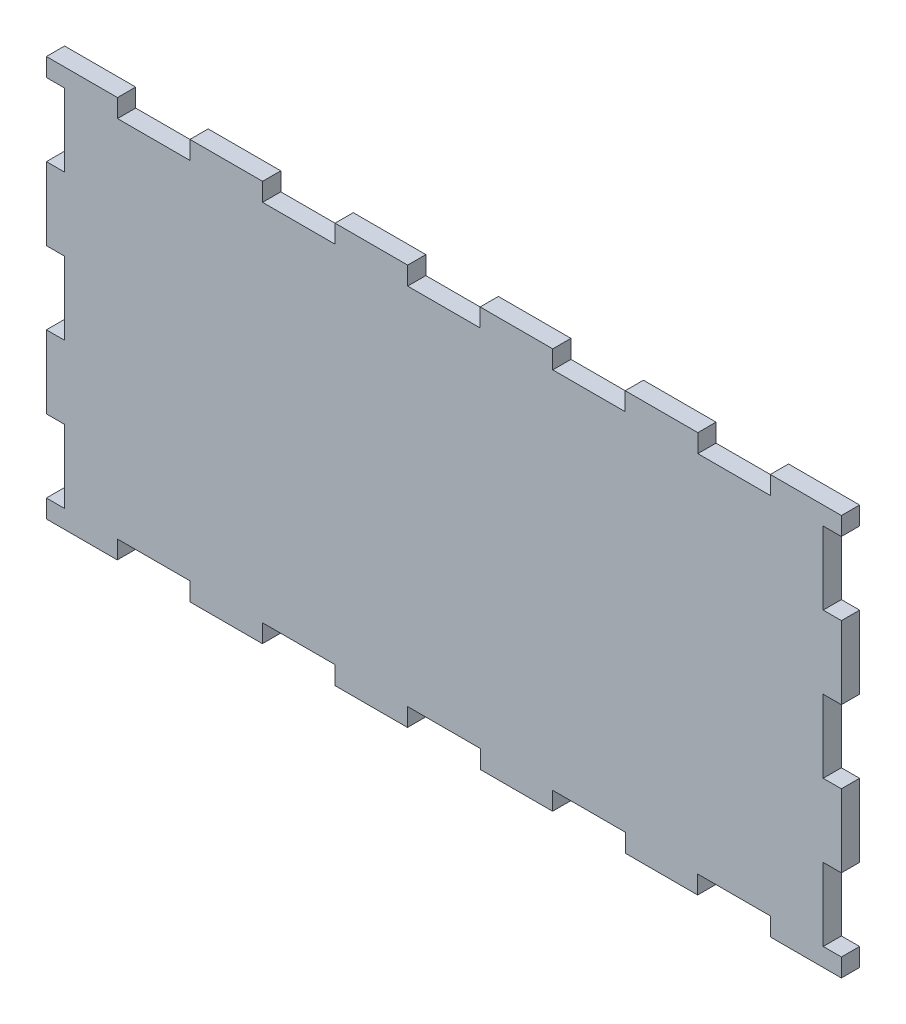
SolidWorks part; units mm, degrees
ref_plane "Front Plane" through (0, 0, 0) normal (0, 0, 1) x (1, 0, 0)
ref_plane "Top Plane" through (0, 0, 0) normal (0, 1, 0) x (1, 0, 0)
ref_plane "Right Plane" through (0, 0, 0) normal (1, 0, 0) x (0, 0, -1)
sketch "Sketch2" plane through (0, 0, 0) normal (0, 0, 1) x (1, 0, 0)
  line L0 (-65.4714, 3) -> (-53.7868, 3)
  line L1 (-53.7868, 3) -> (-53.7868, 6)
  line L2 (-53.7868, 6) -> (-41.7868, 6)
  line L3 (-41.7868, 6) -> (-41.7868, 3)
  line L4 (-41.7868, 3) -> (-29.8791, 3)
  line L5 (-29.8791, 3) -> (-29.8791, 6)
  line L6 (-29.8791, 6) -> (-17.8791, 6)
  line L7 (-17.8791, 6) -> (-17.8791, 3)
  line L8 (-17.8791, 3) -> (-5.9714, 3)
  line L9 (-5.9714, 3) -> (-5.9714, 6)
  line L10 (-5.9714, 6) -> (6.0286, 6)
  line L11 (6.0286, 6) -> (6.0286, 3)
  line L12 (6.0286, 3) -> (17.9363, 3)
  line L13 (17.9363, 3) -> (17.9363, 6)
  line L14 (17.9363, 6) -> (29.9363, 6)
  line L15 (29.9363, 6) -> (29.9363, 3)
  line L16 (29.9363, 3) -> (41.844, 3)
  line L17 (41.844, 3) -> (41.844, 6)
  line L18 (41.844, 6) -> (53.844, 6)
  line L19 (53.844, 6) -> (53.844, 3)
  line L20 (53.844, 3) -> (65.5286, 3)
  line L21 (65.5286, 3) -> (65.5286, 69)
  line L22 (-65.4714, 3) -> (-65.4714, 69)
  line L24 (53.8154, 69) -> (65.5286, 69)
  line L25 (53.8154, 66) -> (53.8154, 69)
  line L26 (41.8725, 66) -> (53.8154, 66)
  line L27 (41.8725, 69) -> (41.8725, 66)
  line L28 (29.9077, 69) -> (41.8725, 69)
  line L29 (29.9077, 66) -> (29.9077, 69)
  line L30 (17.9648, 66) -> (29.9077, 66)
  line L31 (17.9648, 69) -> (17.9648, 66)
  line L32 (6, 69) -> (17.9648, 69)
  line L33 (6, 66) -> (6, 69)
  line L34 (-5.9429, 66) -> (6, 66)
  line L35 (-5.9429, 69) -> (-5.9429, 66)
  line L36 (-17.9077, 69) -> (-5.9429, 69)
  line L37 (-17.9077, 66) -> (-17.9077, 69)
  line L38 (-29.8505, 66) -> (-17.9077, 66)
  line L39 (-29.8505, 69) -> (-29.8505, 66)
  line L40 (-41.8154, 69) -> (-29.8505, 69)
  line L41 (-41.8154, 66) -> (-41.8154, 69)
  line L42 (-53.7582, 66) -> (-41.8154, 66)
  line L43 (-53.7582, 69) -> (-53.7582, 66)
  line L44 (-65.4714, 69) -> (-53.7582, 69)
  line M1 (-54, 0) -> (-54, 6)
  line M2 (-54, 6) -> (-62.5, 6)
  line M3 (-62.5, 6) -> (-62.5, 0)
  dimension "D1" = 60
  dimension "D2" = 3
  dimension "D3" = 12
  dimension "D4" = 131
extrude "Boss-Extrude1" add sketch "Sketch2" along normal blind 3 contours L0 M3 M1 M2 | L44 L22 L0 L2 L3 L4 L5 L6 L7 L8 L9 L10 L11 L12 L13 L14 L15 L16 L17 L18 L19 L20 L21 L24 L25 L26 L27 L28 L29 L30 L31 L32 L33 L34 L35 L36 L37 L38 L39 L40 L41 L42 L43 M3 M2
sketch "Sketch3" plane through (0, 0, 3) normal (0, 0, 1) x (1, 0, 0)
  line L0 (-65.4714, 3) -> (-65.4714, 69) construction
  line L1 (-65.4714, 6) -> (-62.4714, 6)
  line L2 (-65.4714, 6) -> (-65.4714, 18)
  line L3 (-65.4714, 18) -> (-62.4714, 18)
  line L4 (-62.4714, 6) -> (-62.4714, 18)
  line L5 (62.5286, 6) -> (62.5286, 18)
  line L6 (62.5286, 6) -> (65.5286, 6)
  line L7 (65.5286, 6) -> (65.5286, 18)
  line L8 (62.5286, 18) -> (65.5286, 18)
  line L9 (62.5286, 30) -> (62.5286, 42)
  line L10 (62.5286, 30) -> (65.5286, 30)
  line L11 (65.5286, 30) -> (65.5286, 42)
  line L12 (62.5286, 42) -> (65.5286, 42)
  line L13 (62.5286, 54) -> (62.5286, 66)
  line L14 (62.5286, 54) -> (65.5286, 54)
  line L15 (65.5286, 54) -> (65.5286, 66)
  line L16 (62.5286, 66) -> (65.5286, 66)
  line L17 (-65.4714, 30) -> (-65.4714, 42)
  line L18 (-65.4714, 30) -> (-62.4714, 30)
  line L19 (-62.4714, 30) -> (-62.4714, 42)
  line L20 (-65.4714, 42) -> (-62.4714, 42)
  line L21 (-65.4714, 54) -> (-65.4714, 66)
  line L22 (-65.4714, 54) -> (-62.4714, 54)
  line L23 (-62.4714, 54) -> (-62.4714, 66)
  line L24 (-65.4714, 66) -> (-62.4714, 66)
  line L25 (65.5286, 3) -> (65.5286, 69) construction
  point P6 (-65.4714, 36)
  line M26 (65.5286, 3) -> (65.5286, 69)
  line M48 (-65.4714, 69) -> (-65.4714, 3)
  dimension "D1" = 12
  dimension "D2" = 3
  dimension "D5" = 12
  dimension "D3" = 2
  dimension "D4" = 3
extrude "Cut-Extrude1" cut sketch "Sketch3" against normal blind 6 contours L24 L22 L23 M48 | L1 L4 L3 M48 | L12 L9 L10 M26 | L8 L5 L6 M26 | L17 L20 L19 L18 | L13 L16 L15 L14
